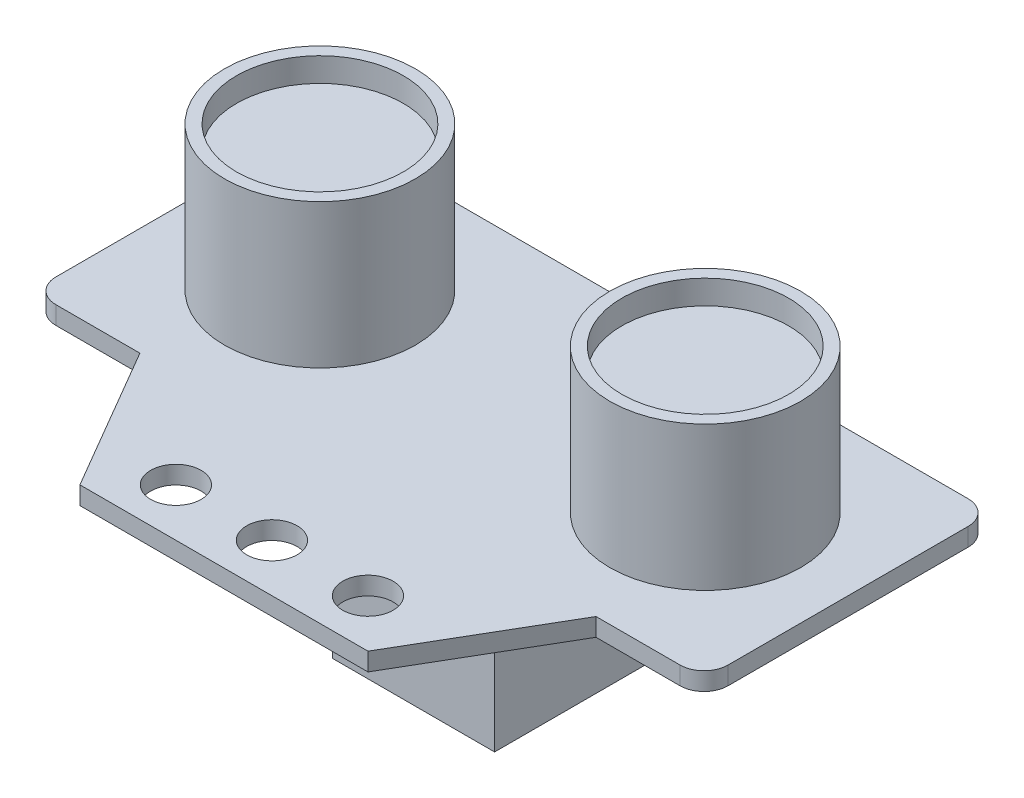
SolidWorks part; units mm, degrees
ref_plane "Front Plane" through (0, 0, 0) normal (0, 0, 1) x (1, 0, 0)
ref_plane "Top Plane" through (0, 0, 0) normal (0, 1, 0) x (1, 0, 0)
ref_plane "Right Plane" through (0, 0, 0) normal (1, 0, 0) x (0, 0, -1)
sketch "Sketch1" plane through (0, 0, 0) normal (0, 1, 0) x (1, 0, 0)
  line L0 (12, 0) -> (-12, 0)
  line L1 (-12, 0) -> (-19, 12)
  line L2 (-19, 12) -> (-28, 12)
  line L3 (-28, 12) -> (-28, 36)
  line L4 (-28, 36) -> (28, 36)
  line L5 (0, 36) -> (0, 0) construction
  line L6 (28, 12) -> (28, 36)
  line L7 (19, 12) -> (28, 12)
  line L8 (12, 0) -> (19, 12)
  line L9 (-8, 4) -> (8, 4) construction
  circle A0 centre (0, 4) radius 2.1
  circle A1 centre (-8, 4) radius 2.1
  circle A2 centre (8, 4) radius 2.1
  dimension "D6" = 4.2
  dimension "D1" = 56
  dimension "D2" = 36
  dimension "D3" = 24
  dimension "D4" = 24
  dimension "D5" = 9
  dimension "D7" = 1.9
  dimension "D8" = 16
extrude "Boss-Extrude1" add sketch "Sketch1" along normal blind 1.5
fillet "Fillet1" radius 2 4 edges at (28, 0.75, -12) (28, 0.75, -36) (-28, 0.75, -36) (-28, 0.75, -12)
sketch "Sketch2" plane through (0, 1.5, 0) normal (0, 1, 0) x (1, 0, 0)
  line L0 (0, 0) -> (0, 36) construction
  line L1 (26, 36) -> (-26, 36) construction
  line L2 (-28, 34) -> (-28, 14) construction
  circle A0 centre (-16.05, 24.05) radius 7.95
  circle A1 centre (16.05, 24.05) radius 7.95
  dimension "D1" = 15.9
  dimension "D2" = 4
  dimension "D3" = 4
extrude "Boss-Extrude2" add sketch "Sketch2" along normal blind 12
sketch "Sketch3" plane through (0, 0, 0) normal (0, -1, 0) x (1, 0, 0)
  line L0 (26, -36) -> (-26, -36) construction
  line L1 (-6.75, -15.8) -> (6.75, -15.8)
  line L2 (-6.75, -15.8) -> (-6.75, -31.8)
  line L3 (-6.75, -31.8) -> (6.75, -31.8)
  line L4 (6.75, -15.8) -> (6.75, -31.8)
  point P4 (0, -15.8)
  dimension "D1" = 13.5
  dimension "D2" = 16
  dimension "D3" = 4.2
extrude "Boss-Extrude3" add sketch "Sketch3" along normal blind 16.3
sketch "Sketch4" plane through (0, 13.5, 0) normal (0, 1, 0) x (1, 0, 0)
  circle A3 centre (-16.05, 24.05) radius 6.95
  circle A4 centre (-16.05, 24.05) radius 6.95
  circle A6 centre (16.05, 24.05) radius 6.95
  circle A7 centre (16.05, 24.05) radius 6.95
  dimension "D1" = 1
  dimension "D2" = 1
extrude "Cut-Extrude1" cut sketch "Sketch4" against normal blind 2
equation "\"width\"= 24"
equation "\"thk\"= 3"
equation "\"holesize\"= 4.2"
equation "\"holedistance\"= ( 20 + 12 ) / 2"
equation "\"threaded_hole\"= 3.9"
equation "\"fillet_radius\"= 2"
equation "\"ground_clearance\"= 25"
equation "\"tire_thk\"= 3"
equation "\"innerwheel_diam\" = \"wheel_diam\"-2*\"tire_thk\""
equation "\"innerwheel_thk\"= 8"
equation "\"wheel_diam\"= 2*(\"width\"/2+\"ground_clearance\")"
equation "\"D6@Sketch1\"=\"holesize\""
equation "\"D8@Sketch1\"=\"holedistance\""
